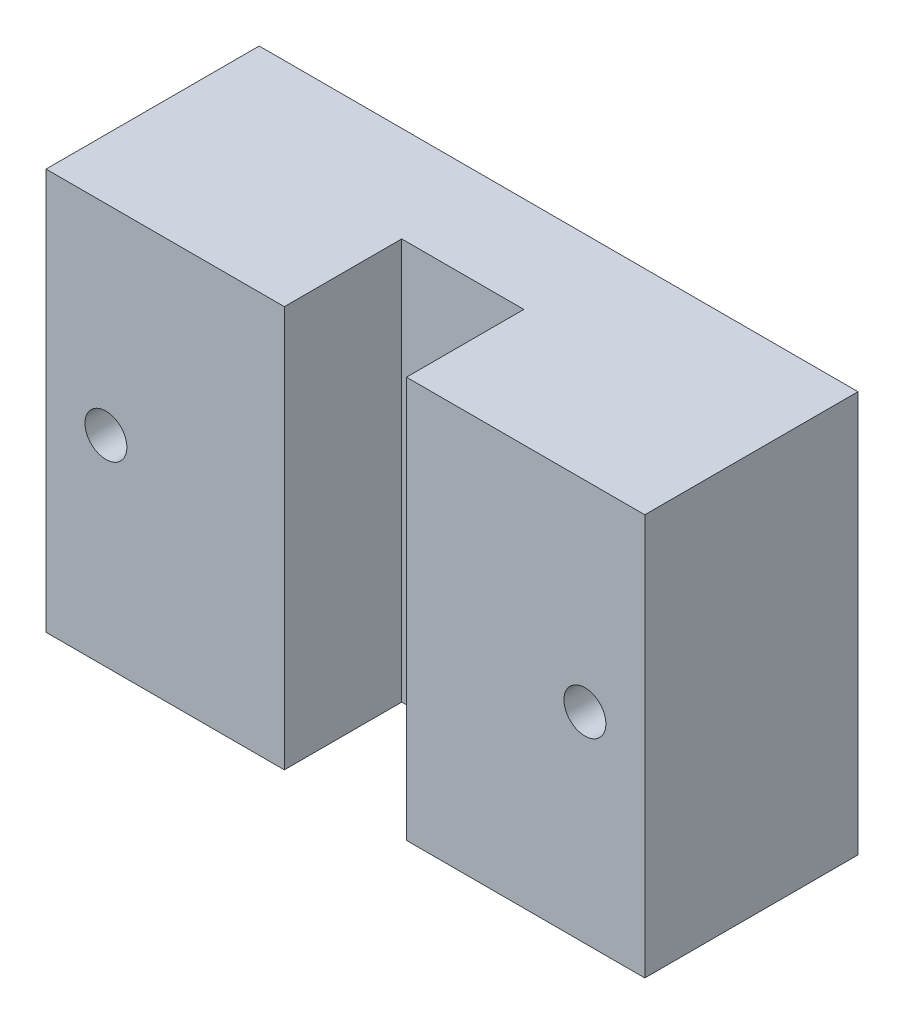
SolidWorks part; units mm, degrees
ref_plane "Спереди" through (0, 0, 0) normal (0, 0, 1) x (1, 0, 0)
ref_plane "Сверху" through (0, 0, 0) normal (0, 1, 0) x (1, 0, 0)
ref_plane "Справа" through (0, 0, 0) normal (1, 0, 0) x (0, 0, -1)
sketch "Sketch2" plane through (0, 0, 0) normal (0, 0, 1) x (1, 0, 0)
  line L0 (20, 0) -> (-20, 0) construction
  line L1 (25, -16.75) -> (-25, -16.75)
  line L2 (25, -16.75) -> (25, 16.75)
  line L3 (25, 16.75) -> (-25, 16.75)
  line L4 (-25, -16.75) -> (-25, 16.75)
  line L5 (25, -16.75) -> (-25, 16.75) construction
  line L6 (25, 16.75) -> (-25, -16.75) construction
  circle A0 centre (-20, 0) radius 1.75
  circle A1 centre (20, 0) radius 1.75
  point P0 (0, 0)
  point P9 (0, 0)
  dimension "D4" = 3.5
  dimension "D1" = 33.5
  dimension "D2" = 50
  dimension "D3" = 40
extrude "Boss-Extrude1" add sketch "Sketch2" along normal blind 8
sketch "Sketch5" plane through (0, -16.75, 0) normal (0, -1, 0) x (1, 0, 0)
  line L0 (-25, 8) -> (-25, 17.8)
  line L1 (-25, 8) -> (25, 8) construction
  line L2 (-25, 17.8) -> (-5.1, 17.8)
  line L3 (-5.1, 17.8) -> (-5.1, 8)
  line L4 (-5.1, 8) -> (5.1, 8)
  line L5 (5.1, 8) -> (5.1, 17.8)
  line L6 (5.1, 17.8) -> (25, 17.8)
  line L7 (25, 17.8) -> (25, 8)
  line L8 (25, 8) -> (-25, 8) construction
  line L9 (-25, 0) -> (25, 0) construction
  line L10 (0, 8) -> (0, 0) construction
  line L11 (-25, 8) -> (-25, 0) construction
  arc A0 (-25, 8) -> (25, 8) centre (0, 43.0625) ccw
  point P17 (0, 0)
  dimension "D1" = 10.2
  dimension "D3" = 9.8
extrude "Boss-Extrude2" add sketch "Sketch5" against normal up to surface (33.5 mm away) up to face at (0, 16.75, 4)
sketch "Sketch6" plane through (0, 0, 0) normal (0, 0, -1) x (-1, 0, 0)
  circle A0 centre (20, 0) radius 1.75
  circle A1 centre (-20, 0) radius 1.75
  circle A3 centre (-20, 0) radius 1.75 construction
extrude "Cut-Extrude1" cut sketch "Sketch6" against normal through all
